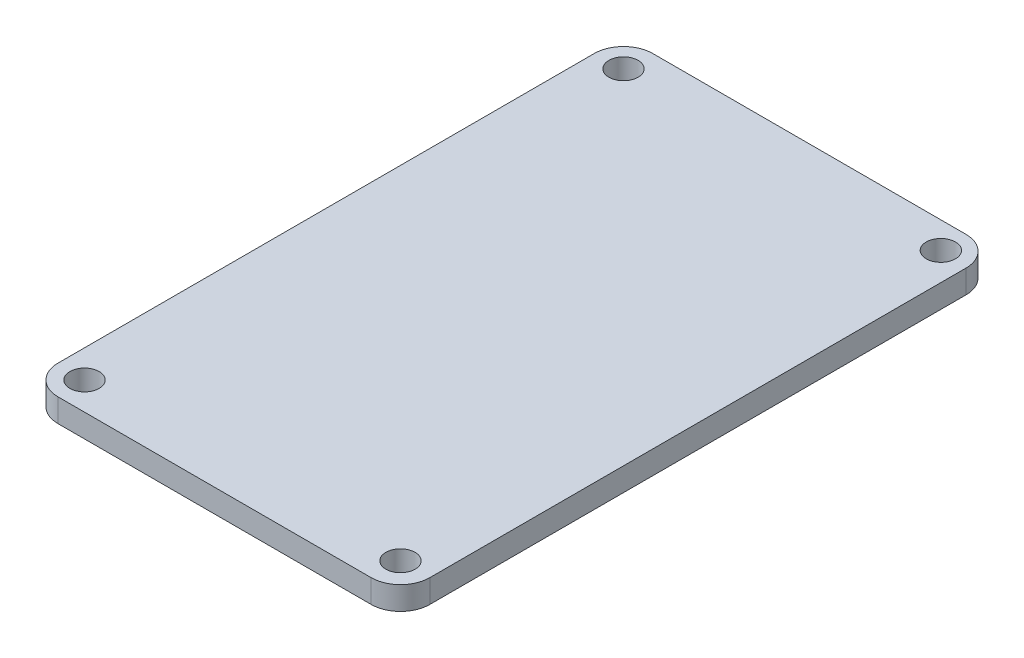
SolidWorks part; units mm, degrees
ref_plane "Front Plane" through (0, 0, 0) normal (0, 0, 1) x (1, 0, 0)
ref_plane "Top Plane" through (0, 0, 0) normal (0, 1, 0) x (1, 0, 0)
ref_plane "Right Plane" through (0, 0, 0) normal (1, 0, 0) x (0, 0, -1)
sketch "Sketch1" plane through (0, 0, 0) normal (0, 1, 0) x (1, 0, 0)
  line L1 (-10.7, -20.32) -> (10.7, -20.32)
  line L2 (-12.7, -18.32) -> (-12.7, 18.32)
  line L3 (-10.7, 20.32) -> (10.7, 20.32)
  line L4 (12.7, -18.32) -> (12.7, 18.32)
  line L5 (-12.7, -20.32) -> (12.7, 20.32) construction
  line L6 (-12.7, 20.32) -> (12.7, -20.32) construction
  line L7 (-10.16, -20.32) -> (10.16, -20.32) construction
  line L8 (-10.16, -20.32) -> (-10.16, 20.32) construction
  line L9 (-10.16, 20.32) -> (10.16, 20.32) construction
  line L10 (10.16, -20.32) -> (10.16, 20.32) construction
  line L11 (-10.16, -20.32) -> (10.16, 20.32) construction
  line L12 (-10.16, 20.32) -> (10.16, -20.32) construction
  arc A0 (-12.7, -18.32) -> (-10.7, -20.32) centre (-10.7, -18.32) ccw
  arc A1 (10.7, -20.32) -> (12.7, -18.32) centre (10.7, -18.32) ccw
  arc A2 (12.7, 18.32) -> (10.7, 20.32) centre (10.7, 18.32) ccw
  arc A3 (-10.7, 20.32) -> (-12.7, 18.32) centre (-10.7, 18.32) ccw
  point P0 (0, 0)
  point P18 (0, 0)
  dimension "D3" = 2
  dimension "D1" = 40.64
  dimension "D2" = 25.4
  dimension "D4" = 40.64
  dimension "D5" = 20.32
extrude "Boss-Extrude1" add sketch "Sketch1" along normal blind 1.5875
hole_wizard "Ø2.0mm Dowel Hole1" positions "Sketch9" profile "Sketch4" hole size "Ø2.0" standard "ANSI Metric"
sketch "Sketch9" plane through (0, 1.5875, 0) normal (0, 1, 0) x (1, 0, 0)
  line L0 (10.7, 20.32) -> (-10.7, 20.32) construction
  line L2 (-10.7, -20.32) -> (10.7, -20.32) construction
  line L3 (12.7, -18.32) -> (12.7, 18.32) construction
  point P0 (-10.7948, 18.415)
  point P2 (10.795, 18.51)
  point P4 (10.7, -18.32)
  point P7 (-10.7948, -18.415)
  dimension "D1" = 21.59
  dimension "D2" = 36.83
  dimension "D3" = 1.905
  dimension "D4" = 1.905
  dimension "D5" = 36.83
  dimension "D6" = 1.905
sketch "Sketch4" plane through (-10.7948, 1.5875, -18.415) normal (1, 0, 0) x (0, 0, 1)
  line L0 (0, 0) -> (0, 38.7009)
  line L1 (0, 38.7009) -> (1, 38.1)
  line L2 (1, 38.1) -> (1, 0)
  line L5 (1, 0) -> (0, 0)
  line L10 (0, 38.7009) -> (-1, 38.1) construction
  line L11 (0, -6.35) -> (0, 107.95) construction
  dimension "Hole Dia." = 2
  dimension "Hole Depth" = 38.1
  dimension "Drill Angle" = 118
